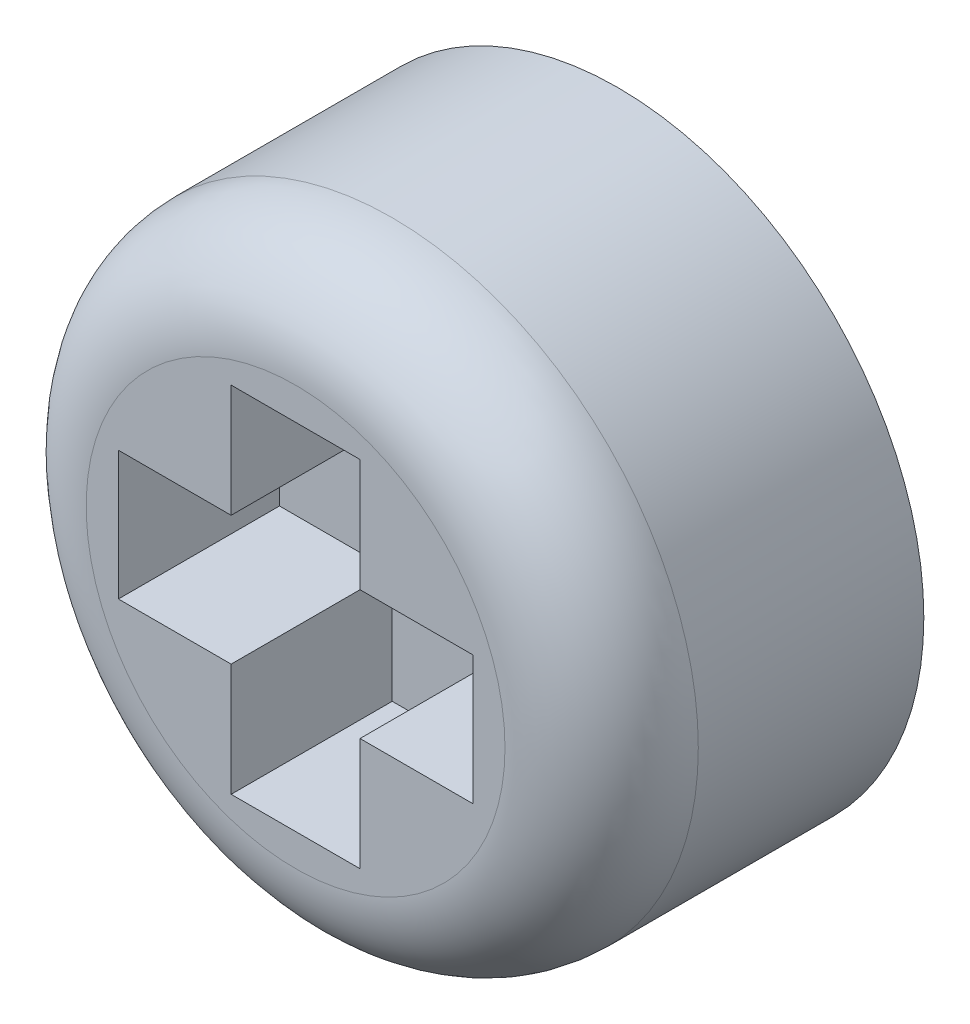
SolidWorks part; units mm, degrees
ref_plane "Front Plane" through (0, 0, 0) normal (0, 0, 1) x (1, 0, 0)
ref_plane "Top Plane" through (0, 0, 0) normal (0, 1, 0) x (1, 0, 0)
ref_plane "Right Plane" through (0, 0, 0) normal (1, 0, 0) x (0, 0, -1)
sketch "Sketch1" plane through (0, 0, 0) normal (0, 0, 1) x (1, 0, 0)
  circle A0 centre (0, 0) radius 2.413
extrude "Boss-Extrude1" add sketch "Sketch1" along normal blind 2.54
sketch "Sketch2" plane through (0, 0, 2.54) normal (0, 0, 1) x (1, 0, 0)
  line L0 (-0.508, 0.508) -> (-0.508, 1.397)
  line L1 (0.508, 0.508) -> (1.397, 0.508)
  line L2 (0.508, -1.397) -> (0.508, -0.508)
  line L3 (-1.397, -0.508) -> (-0.508, -0.508)
  line L4 (-0.508, -1.397) -> (-0.508, -0.508)
  line L5 (-1.397, 0.508) -> (-0.508, 0.508)
  line L6 (-1.397, -0.508) -> (-1.397, 0.508)
  line L7 (-0.508, -1.397) -> (0.508, -1.397)
  line L8 (1.397, -0.508) -> (1.397, 0.508)
  line L9 (0.508, 1.397) -> (-0.508, 1.397)
  line L10 (0.508, 0.508) -> (0.508, 1.397)
  line L11 (0.508, -0.508) -> (1.397, -0.508)
extrude "Cut-Extrude1" cut sketch "Sketch2" against normal blind 1.27
fillet "Fillet1" radius 0.762 1 edges at (2.413, 0, 2.54)
